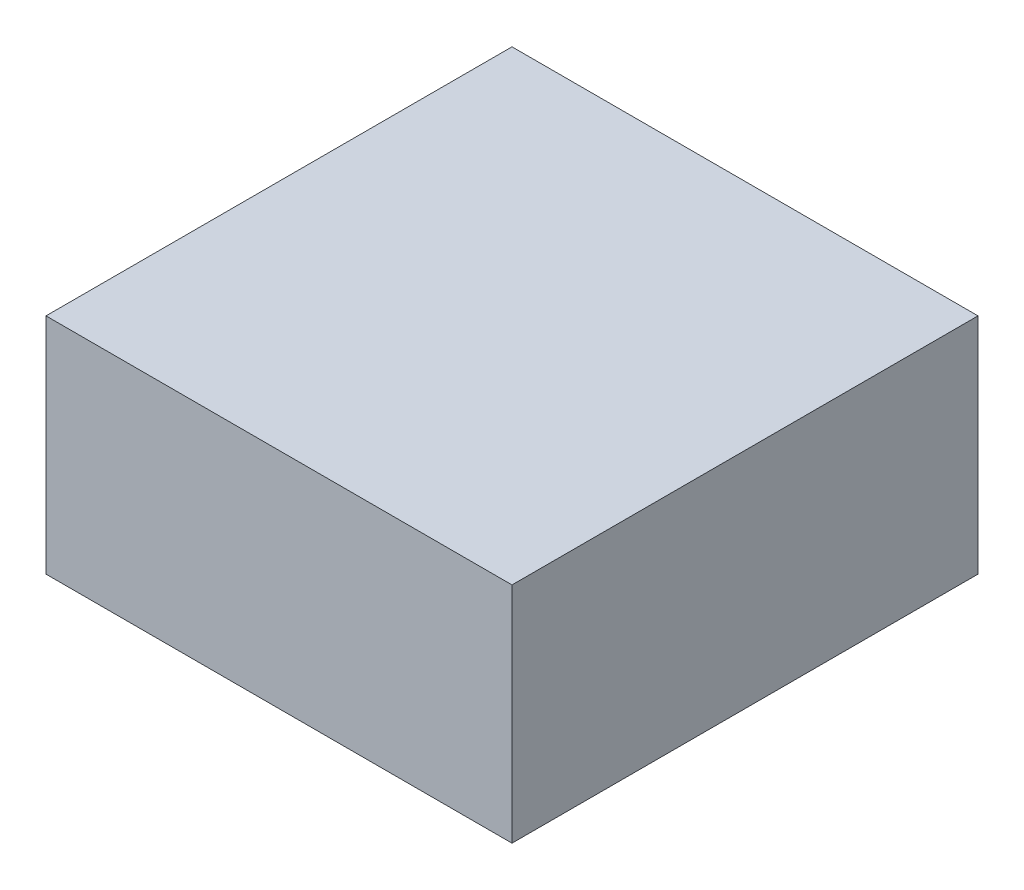
SolidWorks part; units mm, degrees
material "Glass"
ref_plane "Front Plane" through (0, 0, 0) normal (0, 0, 1) x (1, 0, 0)
ref_plane "Top Plane" through (0, 0, 0) normal (0, 1, 0) x (1, 0, 0)
ref_plane "Right Plane" through (0, 0, 0) normal (1, 0, 0) x (0, 0, -1)
sketch "Sketch1" plane through (0, 0, 0) normal (0, 1, 0) x (1, 0, 0)
  line L1 (-6.35, 6.35) -> (6.35, 6.35)
  line L2 (-6.35, 6.35) -> (-6.35, -6.35)
  line L3 (-6.35, -6.35) -> (6.35, -6.35)
  line L4 (6.35, 6.35) -> (6.35, -6.35)
  dimension "D1" = 6.35
  dimension "D2" = 6.35
  dimension "D3" = 6.35
  dimension "D4" = 6.35
extrude "Boss-Extrude1" add sketch "Sketch1" along normal mid plane 6.096
